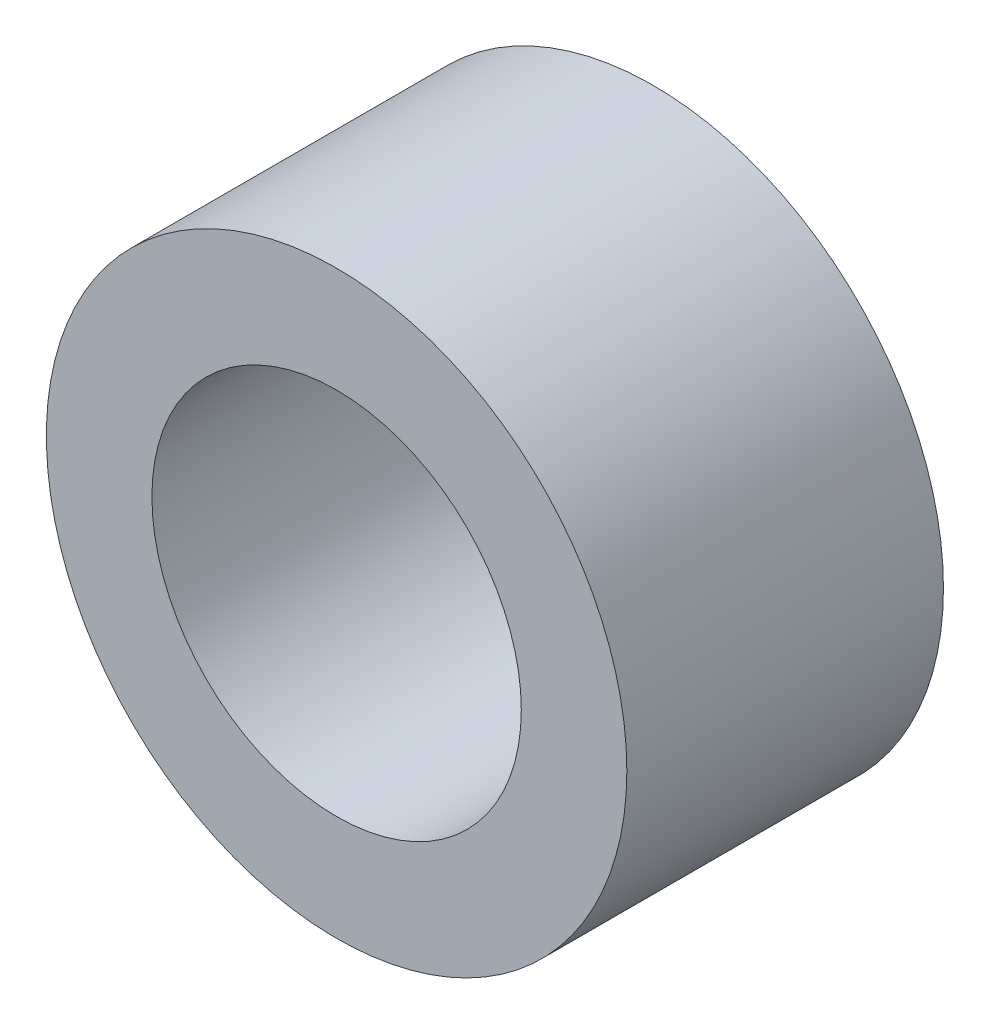
SolidWorks part; units mm, degrees
material "PTFE (general)"
ref_plane "Front Plane" through (0, 0, 0) normal (0, 0, 1) x (1, 0, 0)
ref_plane "Top Plane" through (0, 0, 0) normal (0, 1, 0) x (1, 0, 0)
ref_plane "Right Plane" through (0, 0, 0) normal (1, 0, 0) x (0, 0, -1)
sketch "Sketch1" plane through (0, 0, 0) normal (0, 0, 1) x (1, 0, 0)
  line L0 (-17.4625, 0) -> (17.4625, 0) construction
  line L1 (-11.1125, 0) -> (11.1125, 0) construction
  point P4 (0, 0)
  point P7 (0, 0)
  dimension "OD" = 34.925
  dimension "ID" = 22.225
  dimension "Wall Thickness" = 6.35
sketch "Sketch2" plane through (0, 0, 0) normal (1, 0, 0) x (0, 0, -1)
  line L0 (9.525, 0) -> (-9.525, 0) construction
  point P0 (42.8625, 0)
  point P4 (0, 0)
  point P6 (-42.8625, 0)
  dimension "D1" = 19.05
  dimension "D2" = 52.3875
  dimension "D3" = 52.3875
sketch "Sketch3" plane through (0, 0, 0) normal (0, 0, 1) x (1, 0, 0)
  circle A0 centre (0, 0) radius 17.4625
  circle A1 centre (0, 0) radius 11.1125
  dimension "D1" = 34.925
extrude "Boss-Extrude1" add sketch "Sketch3" along normal mid plane 19.05
equation "\"D2@Sketch2\"=\"OD@Sketch1\" * 1.5"
equation "\"D3@Sketch2\"=\"D2@Sketch2\""
equation "\"D1@Sketch3\" = \"OD@Sketch1\""
equation "\"D1@Boss-Extrude1\"=\"D1@Sketch2\""
